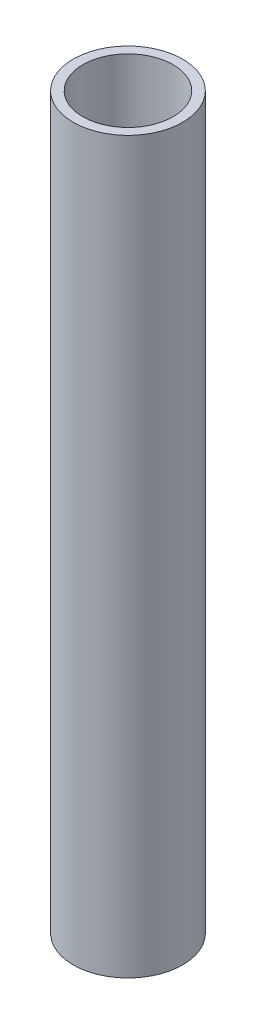
SolidWorks part; units mm, degrees
ref_plane "Plan de face" through (0, 0, 0) normal (0, 0, 1) x (1, 0, 0)
ref_plane "Plan de dessus" through (0, 0, 0) normal (0, 1, 0) x (1, 0, 0)
ref_plane "Plan de droite" through (0, 0, 0) normal (1, 0, 0) x (0, 0, -1)
sketch "Esquisse1" plane through (0, 0, 0) normal (0, 1, 0) x (1, 0, 0)
  circle A0 centre (0, 0) radius 2.35
  circle A1 centre (0, 0) radius 2.85
  dimension "D1" = 5.7
  dimension "D2" = 0.5
extrude "Boss.-Extru.1" add sketch "Esquisse1" along normal blind 38
